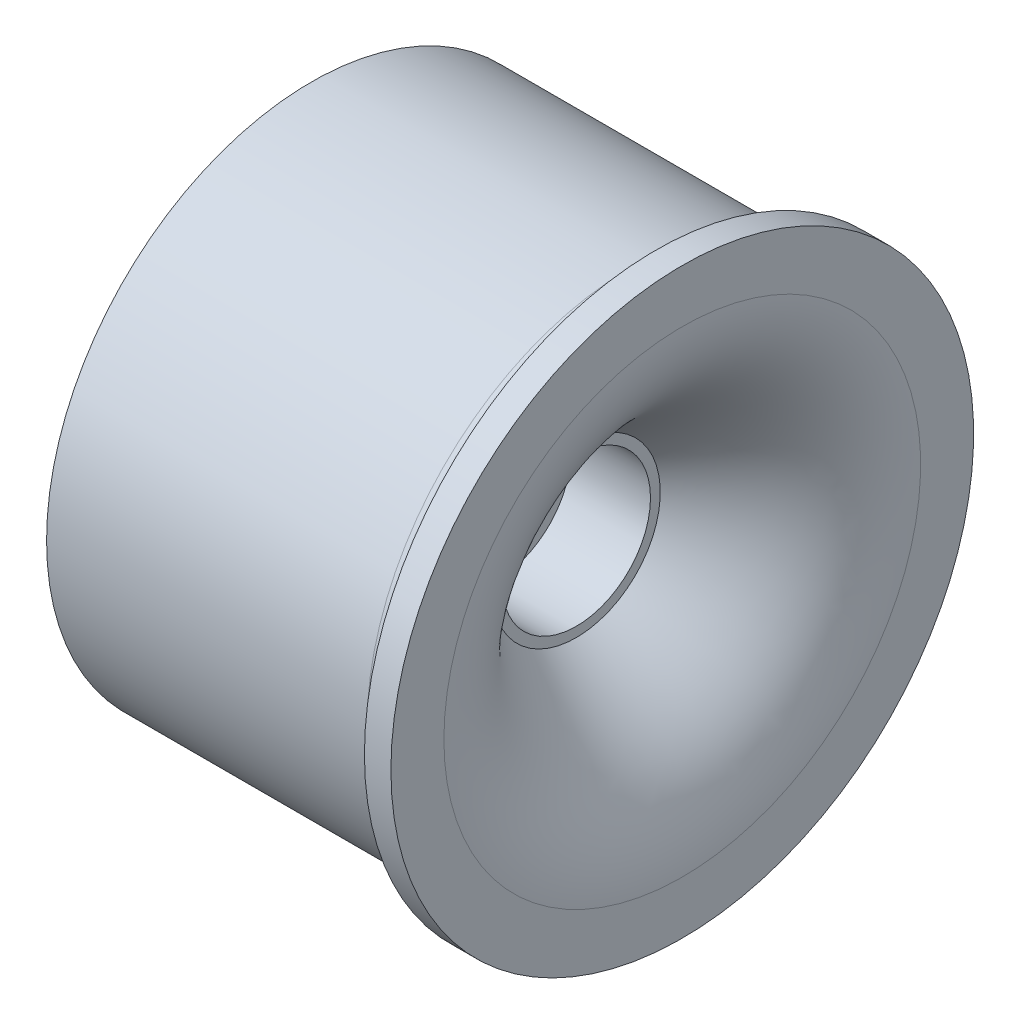
SolidWorks part; units mm, degrees
ref_plane "Front Plane" through (0, 0, 0) normal (0, 0, 1) x (1, 0, 0)
ref_plane "Top Plane" through (0, 0, 0) normal (0, 1, 0) x (1, 0, 0)
ref_plane "Right Plane" through (0, 0, 0) normal (1, 0, 0) x (0, 0, -1)
sketch "Sketch1" plane through (0, 0, 0) normal (0, 0, 1) x (1, 0, 0)
  line L0 (0, 0) -> (9.2832, 0) construction
  line L1 (0, 0) -> (0, 12.5101) construction
  line L2 (-7, 9) -> (5, 9)
  line L3 (7, 9) -> (7, 11)
  line L4 (7, 11) -> (6, 11)
  line L5 (6, 11) -> (6, 10.9)
  line L6 (5.1, 10) -> (-5.1, 10)
  line L7 (-6, 11) -> (-6, 10.9)
  line L8 (-7, 9) -> (-7, 11)
  line L9 (-7, 11) -> (-6, 11)
  line L10 (7, 7.7504) -> (7, 10.2496) construction
  line L11 (0, 3.4277) -> (0, 1)
  arc A0 (6, 10.9) -> (5.1, 10) centre (5.1, 10.9) cw
  arc A1 (-6, 10.9) -> (-5.1, 10) centre (-5.1, 10.9) ccw
  spline S0 degree 3 poles (7, 9) (7, 7.438) (5.4512, 4.5818) (0.0016, 1.0014) (0, 1) knots 0 0 0 0 0.405902 1 1 1 1
  spline S1 degree 1 poles (5, 9) (-1.3066, 2.5142) knots 0 0 1 1 construction
  spline S2 degree 3 poles (5, 9) (5, 8.8565) (4.9806, 8.5526) (4.8799, 8.0859) (4.6375, 7.5283) (3.996, 6.6902) (2.861, 5.6187) (1.4785, 4.504) (0.3776, 3.6936) (-0.3403, 3.187) (-0.6931, 2.9443) (-0.9015, 2.803) (-0.9975, 2.7385) (-1.052, 2.7022) (-1.0762, 2.6861) (-1.0898, 2.6771) (-1.0958, 2.6731) (-1.0996, 2.6706) (-1.1017, 2.6692) (-1.104, 2.6677) (-1.1061, 2.6663) (-1.1095, 2.664) (-1.1133, 2.6615) (-1.1194, 2.6574) (-1.1263, 2.6527) (-1.1365, 2.6457) (-1.1506, 2.6359) (-1.1702, 2.6222) (-1.2098, 2.5927) (-1.2456, 2.5652) (-1.2886, 2.5297) (-1.3066, 2.5142) knots 0 0 0 0 0.0625 0.125 0.25 0.375 0.5 0.625 0.75 0.8125 0.875 0.90625 0.9375 0.953125 0.96875 0.976562 0.984375 0.988281 0.992188 0.994141 0.996094 0.99707 0.998047 0.998535 0.999023 0.999268 0.999512 0.999756 0.999878 0.999939 1 1 1 1 only from (5, 9) to (0, 3.4277)
  point P12 (6, 10)
  point P16 (0, 10)
  point P18 (0, 9)
  point P22 (4.6416, 0)
  dimension "D5" = 0.9
  dimension "D1" = 7
  dimension "D2" = 2
  dimension "D3" = 1
  dimension "D4" = 1
  dimension "D6" = 10
  dimension "D7" = 1
  dimension "D8" = 5
  dimension "D9" = 2
revolve "Revolve1" add sketch "Sketch1" angle 360 about L0
sketch "Sketch2" plane through (-7, 0, 0) normal (-1, 0, 0) x (0, 0, 1)
  circle A0 centre (0, 0) radius 1 construction
  circle A1 centre (0, 0) radius 1
  circle A3 centre (0, 0) radius 5.5
  dimension "D1" = 11
extrude "Boss-Extrude1" add sketch "Sketch2" against normal blind 10
sketch "Sketch3" plane through (3, 0, 0) normal (1, 0, 0) x (0, 0, -1)
  circle A0 centre (0, 0) radius 2.8
  dimension "D1" = 5.6
extrude "Cut-Extrude1" cut sketch "Sketch3" against normal blind 3
sketch "Sketch4" plane through (-7, 0, 0) normal (-1, 0, 0) x (0, 0, 1)
  circle A0 centre (0, 0) radius 1.42
  dimension "D1" = 2.84
extrude "Cut-Extrude2" cut sketch "Sketch4" against normal blind 7
sketch "Sketch5" plane through (0, 0, 0) normal (1, 0, 0) x (0, 0, -1)
  circle A0 centre (0, 0) radius 10 construction
  circle A1 centre (0, 0) radius 10
  circle A2 centre (0, 0) radius 22.1317
extrude "Cut-Extrude3" cut sketch "Sketch5" against normal blind 10
